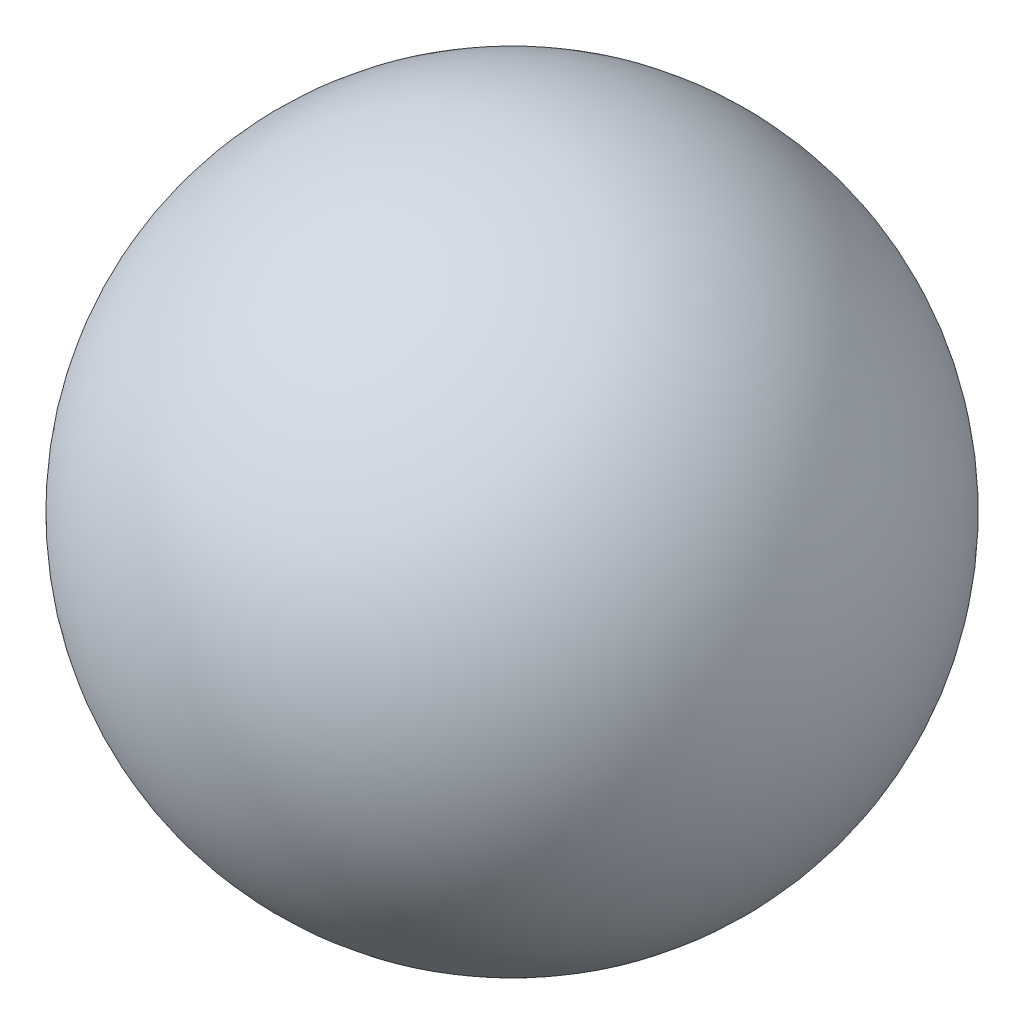
SolidWorks part; units mm, degrees
ref_plane "Front Plane" through (0, 0, 0) normal (0, 0, 1) x (1, 0, 0)
ref_plane "Top Plane" through (0, 0, 0) normal (0, 1, 0) x (1, 0, 0)
ref_plane "Right Plane" through (0, 0, 0) normal (1, 0, 0) x (0, 0, -1)
sketch "Sketch1" plane through (0, 0, 0) normal (0, 0, 1) x (1, 0, 0)
  line L2 (0, -19.05) -> (0, 19.05)
  arc A0 (0, 19.05) -> (0, -19.05) centre (0, 0) ccw
  dimension "D1" = 19.05
ref_axis "Axis2" through (0, 41.4379, 0) along (0, -1, 0)
revolve "Revolve5" add sketch "Sketch1" angle 360 about axis through (0, 41.4379, 0) along (0, -1, 0)
equation "\"D1@Sketch1\" = \"radius\""
equation "\"radius\"=\"0.75\""
